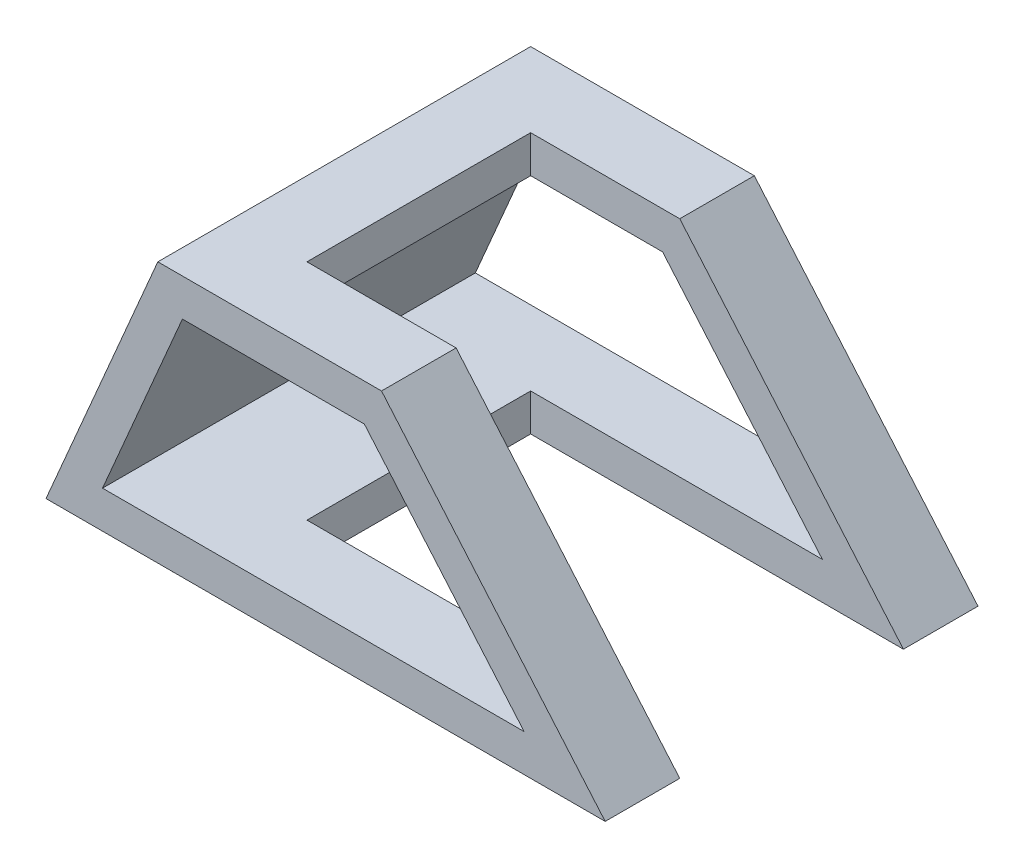
SolidWorks part; units mm, degrees
material "AISI 1020"
ref_plane "Plan de face" through (0, 0, 0) normal (0, 0, 1) x (1, 0, 0)
ref_plane "Plan de dessus" through (0, 0, 0) normal (0, 1, 0) x (1, 0, 0)
ref_plane "Plan de droite" through (0, 0, 0) normal (1, 0, 0) x (0, 0, -1)
sketch "Esquisse1" plane through (0, 0, 0) normal (0, 0, 1) x (1, 0, 0)
  line L0 (0, 0) -> (150, 0)
  line L1 (150, 0) -> (90, 70)
  line L2 (90, 70) -> (30, 70)
  line L3 (30, 70) -> (0, 0)
  line L4 (36.594, 60) -> (15.1654, 10)
  line L5 (15.1654, 10) -> (128.2578, 10)
  line L6 (128.2578, 10) -> (85.4007, 60)
  line L7 (85.4007, 60) -> (36.594, 60)
  dimension "D1" = 150
  dimension "D2" = 70
  dimension "D3" = 30
  dimension "D4" = 60
  dimension "D5" = 60
  dimension "D6" = 10
extrude "Boss.-Extru.2" add sketch "Esquisse1" against normal blind 100
sketch "Esquisse2" plane through (0, 70, 0) normal (0, 1, 0) x (1, 0, 0)
  line L0 (150, 100) -> (150, 0) construction
  line L1 (150, 80) -> (50, 80)
  line L2 (150, 80) -> (150, 20)
  line L3 (150, 20) -> (50, 20)
  line L4 (50, 80) -> (50, 20)
  line L6 (150, 100) -> (90, 100) construction
  dimension "D1" = 60
  dimension "D2" = 100
  dimension "D3" = 20
extrude "Enlèv. mat.-Extru.1" cut sketch "Esquisse2" against normal up to next
